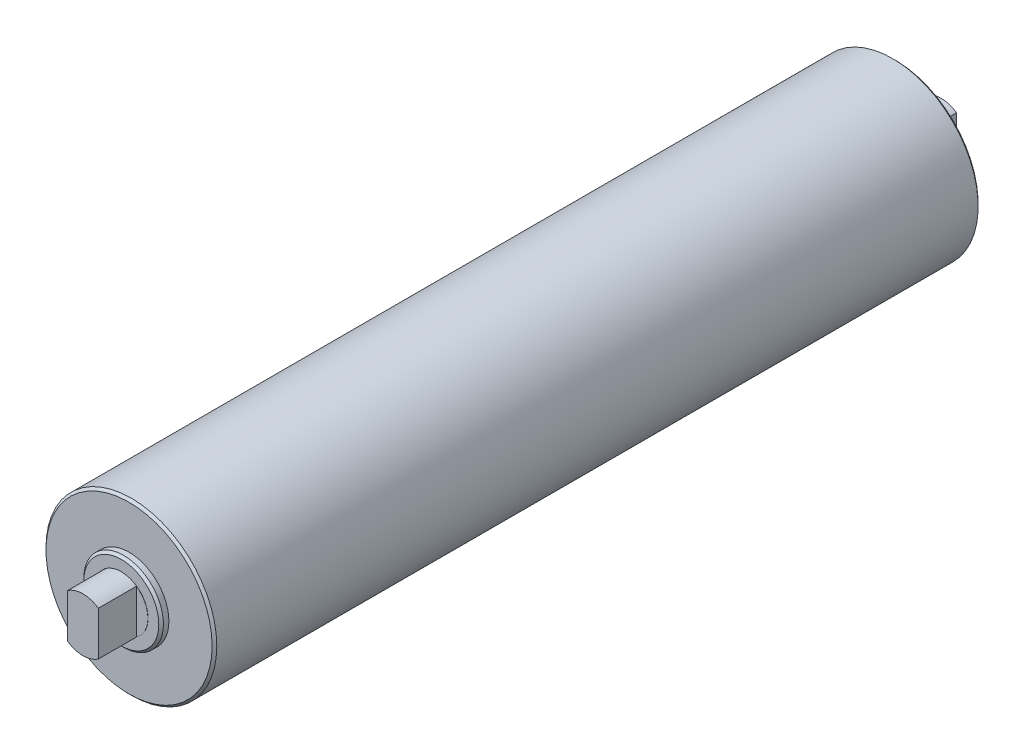
SolidWorks part; units mm, degrees
ref_plane "Front Plane" through (0, 0, 0) normal (0, 0, 1) x (1, 0, 0)
ref_plane "Top Plane" through (0, 0, 0) normal (0, 1, 0) x (1, 0, 0)
ref_plane "Right Plane" through (0, 0, 0) normal (1, 0, 0) x (0, 0, -1)
sketch "Sketch1" plane through (0, 0, 0) normal (0, 0, 1) x (1, 0, 0)
  circle A0 centre (0, 0) radius 55.753
  dimension "D1" = 111.506
extrude "Extrude1" add sketch "Sketch1" along normal blind 250.063
sketch "Sketch2" plane through (0, 0, 250.063) normal (0, 0, 1) x (1, 0, 0)
  circle A0 centre (0, 0) radius 26
  dimension "D1" = 52
extrude "Extrude2" add sketch "Sketch2" along normal blind 5.08
sketch "Sketch3" plane through (0, 0, 255.143) normal (0, 0, 1) x (1, 0, 0)
  circle A0 centre (0, 0) radius 17.5
  dimension "D1" = 35
extrude "Extrude3" add sketch "Sketch3" along normal blind 25.019
sketch "Sketch4" plane through (0, 0, 280.162) normal (0, 0, 1) x (1, 0, 0)
  line L0 (0, 0) -> (0, 31.5292) construction
  line L1 (10.033, 14.3384) -> (10.033, -14.3384)
  line L2 (-17.5, 14.3384) -> (-10.033, 14.3384)
  line L3 (-17.5, 14.3384) -> (-17.5, -14.3384)
  line L4 (-17.5, -14.3384) -> (-10.033, -14.3384)
  line L5 (-10.033, 14.3384) -> (-10.033, -14.3384)
  line L6 (17.5, -14.3384) -> (10.033, -14.3384)
  line L7 (17.5, 14.3384) -> (17.5, -14.3384)
  line L8 (17.5, 14.3384) -> (10.033, 14.3384)
  circle A0 centre (0, 0) radius 17.5 construction
  dimension "D1" = 20.066
extrude "Cut-Extrude1" cut sketch "Sketch4" against normal blind 24.892
chamfer "Chamfer1" distance 1.524 angle 45 2 edges at (26, 0, 255.143) (55.753, 0, 250.063)
mirror "Mirror1" about plane through (0, 0, 0) normal (0, 0, 1) of "Extrude1", "Extrude2", "Extrude3", "Cut-Extrude1", "Chamfer1"
ref_plane "Plane1" [suppressed] through (0, 0, 252) normal (0, 0, 1) x (1, 0, 0)
sketch "Sketch6" [suppressed] plane through (0, 0, 252) normal (0, 0, 1) x (1, 0, 0)
  circle A0 centre (0, 0) radius 20
  dimension "D1" = 40
extrude "Extrude4" [suppressed] add sketch "Sketch6" along normal blind 3 draft 15
sketch "Sketch7" [suppressed] plane through (0, 0, 255) normal (0, 0, 1) x (1, 0, 0)
  line L0 (0, 0) -> (0, -14) construction
  circle A0 centre (0, -14) radius 47.5
  dimension "D1" = 95
  dimension "D2" = 14
extrude "Extrude5" [suppressed] add sketch "Sketch7" along normal blind 41
